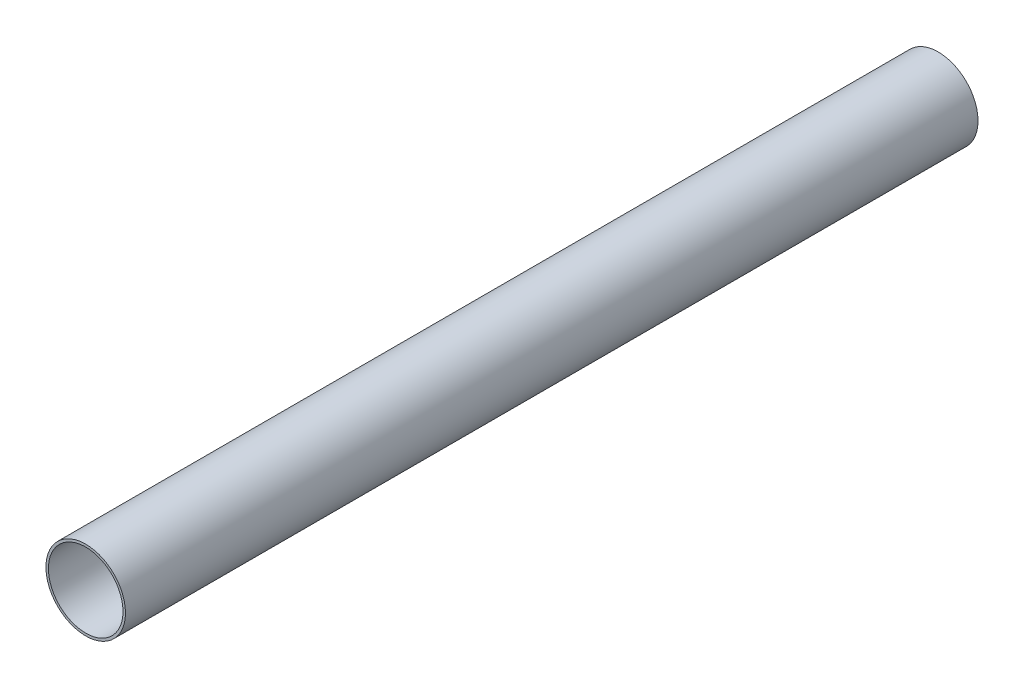
SolidWorks part; units mm, degrees
ref_plane "Front Plane" through (0, 0, 0) normal (0, 0, 1) x (1, 0, 0)
ref_plane "Top Plane" through (0, 0, 0) normal (0, 1, 0) x (1, 0, 0)
ref_plane "Right Plane" through (0, 0, 0) normal (1, 0, 0) x (0, 0, -1)
sketch "Sketch1" plane through (0, 0, 0) normal (0, 0, 1) x (1, 0, 0)
  circle A0 centre (0, 0) radius 22.225
  circle A1 centre (0, 0) radius 23.6982
  dimension "D1" = 44.45
  dimension "D2" = 47.3964
extrude "Boss-Extrude1" add sketch "Sketch1" along normal blind 508
